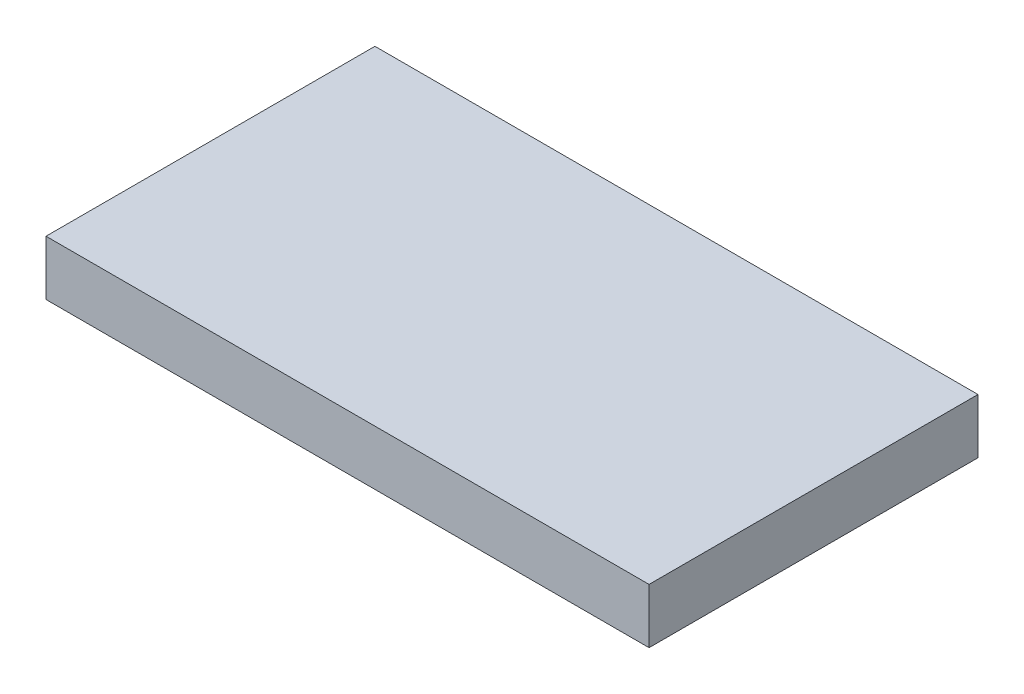
SolidWorks part; units mm, degrees
ref_plane "Front Plane" through (0, 0, 0) normal (0, 0, 1) x (1, 0, 0)
ref_plane "Top Plane" through (0, 0, 0) normal (0, 1, 0) x (1, 0, 0)
ref_plane "Right Plane" through (0, 0, 0) normal (1, 0, 0) x (0, 0, -1)
sketch "Sketch1" plane through (0, 0, 0) normal (0, 1, 0) x (1, 0, 0)
  line L1 (0, 0) -> (110, 0)
  line L2 (0, 0) -> (0, 60)
  line L3 (0, 60) -> (110, 60)
  line L4 (110, 0) -> (110, 60)
extrude "Boss-Extrude1" add sketch "Sketch1" along normal blind 10
